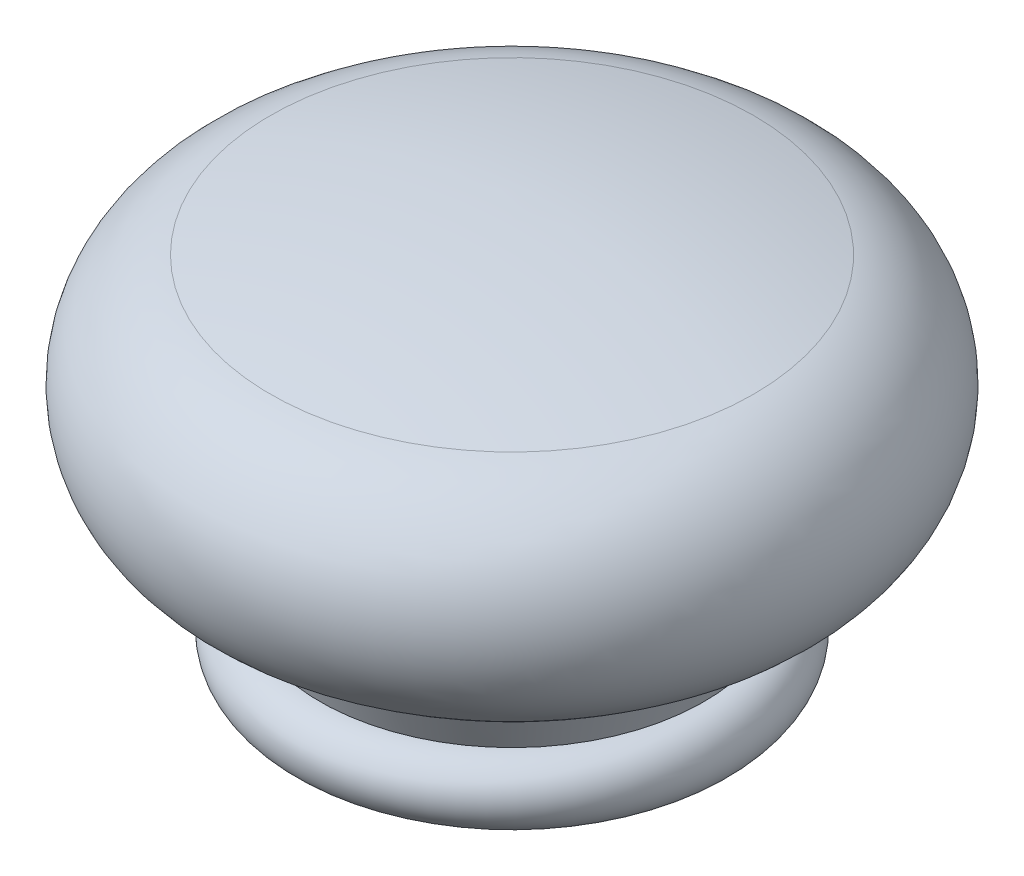
SolidWorks part; units mm, degrees
ref_plane "Alzado" through (0, 0, 0) normal (0, 0, 1) x (1, 0, 0)
ref_plane "Planta" through (0, 0, 0) normal (0, 1, 0) x (1, 0, 0)
ref_plane "Vista lateral" through (0, 0, 0) normal (1, 0, 0) x (0, 0, -1)
sketch "Croquis1" plane through (0, 0, 0) normal (0, 0, 1) x (1, 0, 0)
  line L0 (5, 0) -> (15, 0)
  line L1 (5, 0) -> (5, 10)
  line L2 (0, -10.1653) -> (0, 76.6149) construction
  line L3 (5, 10) -> (0, 10)
  line L4 (17, 9.9994) -> (15, 5)
  line L5 (0, 30) -> (0, 10)
  arc A0 (15, 0) -> (15, 5) centre (15, 2.5) ccw
  arc A1 (17, 9.9994) -> (18.8732, 27.7419) centre (16.75, 18.9959) ccw
  arc A2 (18.8732, 27.7419) -> (0, 30) centre (0, -50) ccw
  dimension "D1" = 2.5
  dimension "D6" = 16.75
  dimension "D7" = 50
  dimension "D8" = 160
  dimension "D9" = 18
  dimension "D2" = 15
  dimension "D3" = 10
  dimension "D4" = 5
  dimension "D5" = 17
  dimension "D10" = 30
revolve "Revolución1" add sketch "Croquis1" angle 360 about L2
